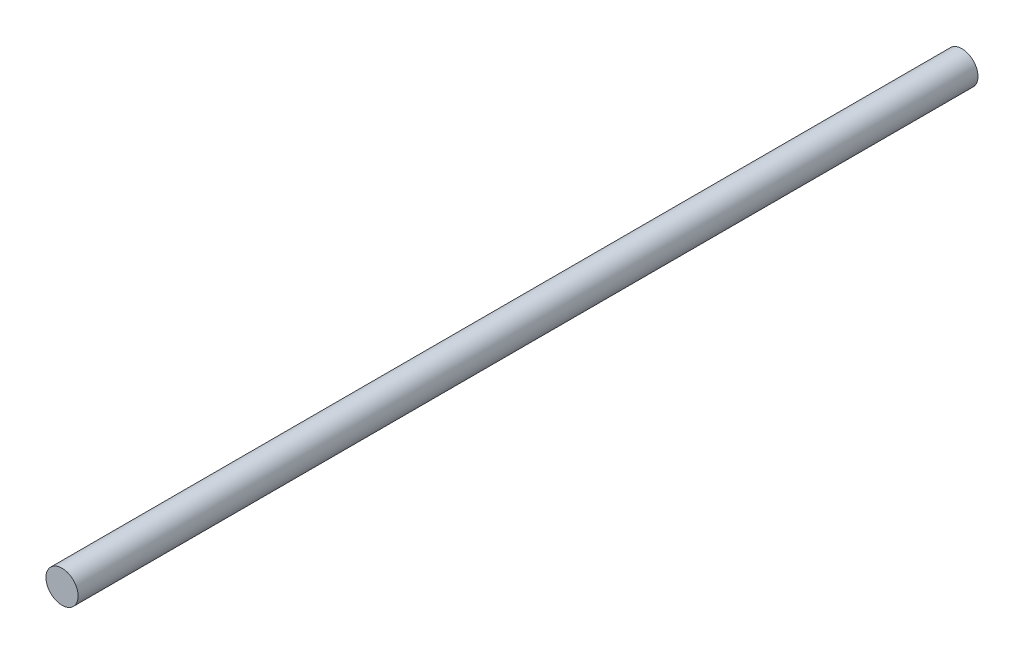
SolidWorks part; units mm, degrees
ref_plane "Front Plane" through (0, 0, 0) normal (0, 0, 1) x (1, 0, 0)
ref_plane "Top Plane" through (0, 0, 0) normal (0, 1, 0) x (1, 0, 0)
ref_plane "Right Plane" through (0, 0, 0) normal (1, 0, 0) x (0, 0, -1)
sketch "Sketch1" plane through (0, 0, 0) normal (0, 0, 1) x (1, 0, 0)
  circle A0 centre (0, 0) radius 15
extrude "Boss-Extrude1" add sketch "Sketch1" along normal blind 840
